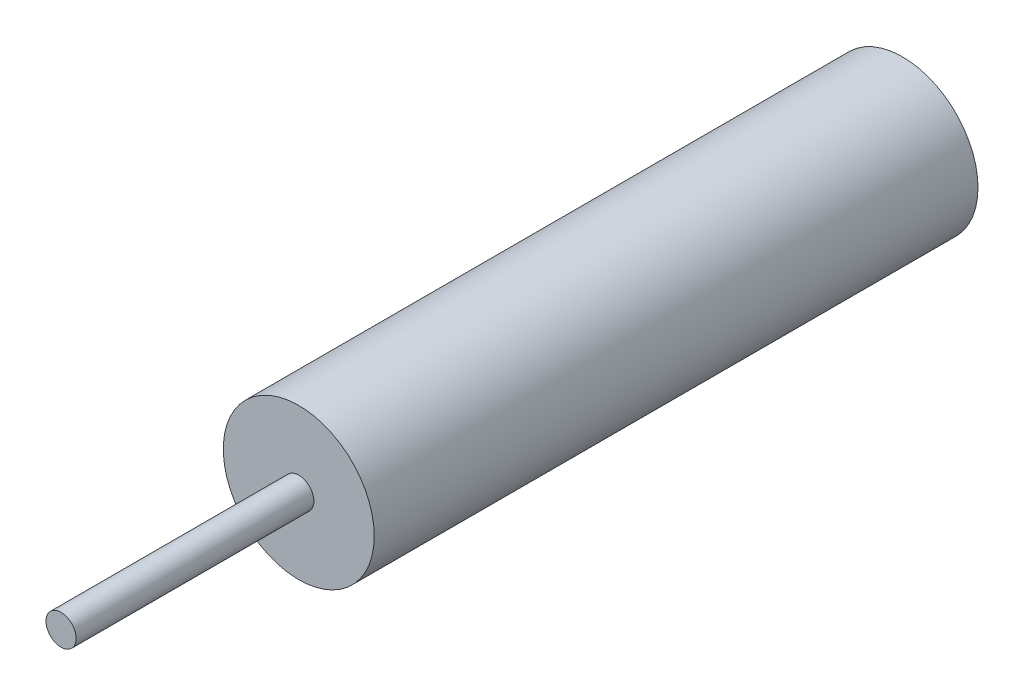
SolidWorks part; units mm, degrees
ref_plane "Front Plane" through (0, 0, 0) normal (0, 0, 1) x (1, 0, 0)
ref_plane "Top Plane" through (0, 0, 0) normal (0, 1, 0) x (1, 0, 0)
ref_plane "Right Plane" through (0, 0, 0) normal (1, 0, 0) x (0, 0, -1)
sketch "Sketch1" plane through (0, 0, 0) normal (0, 0, 1) x (1, 0, 0)
  circle A0 centre (0, 0) radius 3.175
  dimension "D1" = 6.35
extrude "Boss-Extrude1" add sketch "Sketch1" along normal blind 25.4
sketch "Sketch2" plane through (0, 0, 25.4) normal (0, 0, 1) x (1, 0, 0)
  circle A0 centre (0, 0) radius 0.635
  dimension "D1" = 1.27
extrude "Boss-Extrude2" add sketch "Sketch2" along normal blind 10
